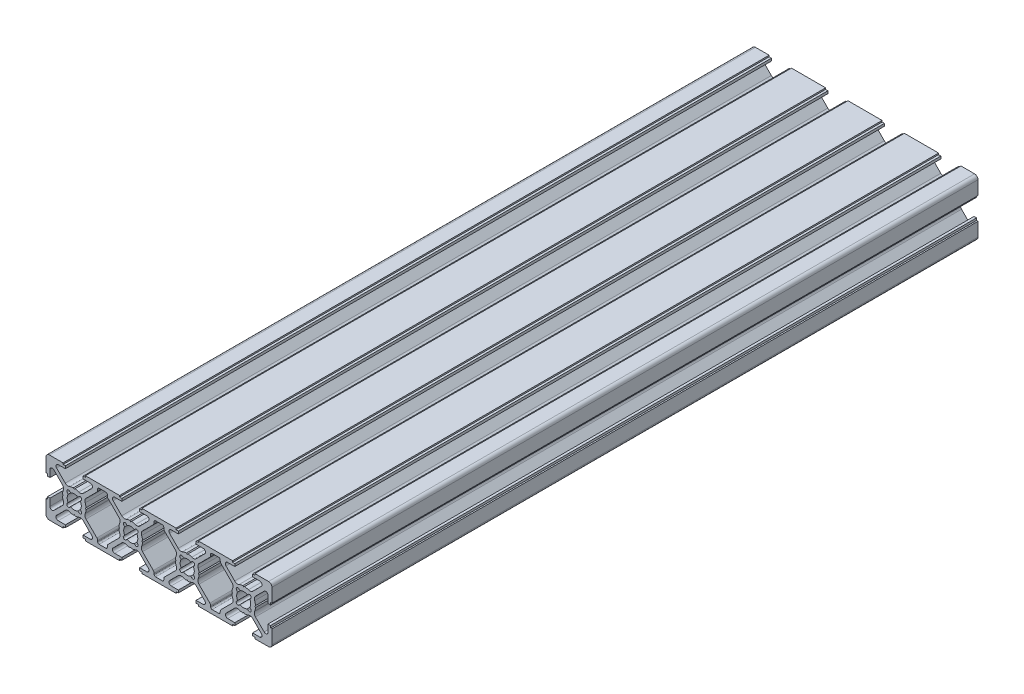
SolidWorks part; units mm, degrees
material "6063-T5"
ref_plane "Ön Düzlem" through (0, 0, 0) normal (0, 0, 1) x (1, 0, 0)
ref_plane "Üst Düzlem" through (0, 0, 0) normal (0, 1, 0) x (1, 0, 0)
ref_plane "Sağ Düzlem" through (0, 0, 0) normal (1, 0, 0) x (0, 0, -1)
sketch "Model" plane through (0, 0, 0) normal (0, 0, 1) x (1, 0, 0)
  line L0 (-8.8, -10) -> (-3.95, -10)
  line L1 (-3.95, -10) -> (-3.95, -9.5)
  line L2 (-3.95, -9.5) -> (-3.1475, -9.5)
  line L3 (-3.1475, -9.5) -> (-3.1475, -8.6)
  line L4 (-3.1475, -8.6) -> (-5.6787, -8.6)
  line L5 (-6.2444, -7.2343) -> (-3.1787, -4.1687)
  line L6 (-0.29, -4.19) -> (0, -3.9)
  line L7 (0, -3.9) -> (0.29, -4.19)
  line L8 (3.1768, -4.1667) -> (6.2444, -7.2343)
  line L9 (5.6787, -8.6) -> (3.1475, -8.6)
  line L10 (3.1475, -8.6) -> (3.1475, -9.5)
  line L11 (3.1475, -9.5) -> (3.95, -9.5)
  line L12 (3.95, -9.5) -> (3.95, -10)
  line L13 (3.95, -10) -> (16.05, -10)
  line L14 (16.05, -10) -> (16.05, -9.5)
  line L15 (16.05, -9.5) -> (16.8525, -9.5)
  line L16 (16.8525, -9.5) -> (16.8525, -8.6)
  line L17 (16.8525, -8.6) -> (14.3213, -8.6)
  line L18 (13.7556, -7.2343) -> (16.8213, -4.1687)
  line L19 (19.71, -4.19) -> (20, -3.9)
  line L20 (20, -3.9) -> (20.29, -4.19)
  line L21 (23.1768, -4.1667) -> (26.2444, -7.2343)
  line L22 (25.6787, -8.6) -> (23.1475, -8.6)
  line L23 (23.1475, -8.6) -> (23.1475, -9.5)
  line L24 (23.1475, -9.5) -> (23.95, -9.5)
  line L25 (23.95, -9.5) -> (23.95, -10)
  line L26 (23.95, -10) -> (36.05, -10)
  line L27 (36.05, -10) -> (36.05, -9.5)
  line L28 (36.05, -9.5) -> (36.8525, -9.5)
  line L29 (36.8525, -9.5) -> (36.8525, -8.6)
  line L30 (36.8525, -8.6) -> (34.3213, -8.6)
  line L31 (33.7556, -7.2343) -> (36.8213, -4.1687)
  line L32 (39.71, -4.19) -> (40, -3.9)
  line L33 (40, -3.9) -> (40.29, -4.19)
  line L34 (43.1768, -4.1667) -> (46.2444, -7.2343)
  line L35 (45.6787, -8.6) -> (43.1475, -8.6)
  line L36 (43.1475, -8.6) -> (43.1475, -9.5)
  line L37 (43.1475, -9.5) -> (43.95, -9.5)
  line L38 (43.95, -9.5) -> (43.95, -10)
  line L39 (43.95, -10) -> (56.05, -10)
  line L40 (56.05, -10) -> (56.05, -9.5)
  line L41 (56.05, -9.5) -> (56.8525, -9.5)
  line L42 (56.8525, -9.5) -> (56.8525, -8.6)
  line L43 (56.8525, -8.6) -> (54.3213, -8.6)
  line L44 (53.7556, -7.2343) -> (56.8213, -4.1687)
  line L45 (59.71, -4.19) -> (60, -3.9)
  line L46 (60, -3.9) -> (60.29, -4.19)
  line L47 (63.1768, -4.1667) -> (66.2444, -7.2343)
  line L48 (65.6787, -8.6) -> (63.1475, -8.6)
  line L49 (63.1475, -8.6) -> (63.1475, -9.5)
  line L50 (63.1475, -9.5) -> (63.95, -9.5)
  line L51 (63.95, -9.5) -> (63.95, -10)
  line L52 (63.95, -10) -> (68.8, -10)
  line L53 (70, -8.8) -> (70, -3.95)
  line L54 (70, -3.95) -> (69.5, -3.95)
  line L55 (69.5, -3.95) -> (69.5, -3.1477)
  line L56 (69.5, -3.1477) -> (68.6, -3.1477)
  line L57 (68.6, -3.1477) -> (68.6, -5.6787)
  line L58 (67.2343, -6.2444) -> (64.1687, -3.1787)
  line L59 (64.19, -0.29) -> (63.9, 0)
  line L60 (63.9, 0) -> (64.19, 0.29)
  line L61 (64.1667, 3.1768) -> (67.2343, 6.2444)
  line L62 (68.6, 5.6787) -> (68.6, 3.1475)
  line L63 (68.6, 3.1475) -> (69.5, 3.1475)
  line L64 (69.5, 3.1475) -> (69.5, 3.95)
  line L65 (69.5, 3.95) -> (70, 3.95)
  line L66 (70, 3.95) -> (70, 8.8)
  line L67 (68.8, 10) -> (63.95, 10)
  line L68 (63.95, 10) -> (63.95, 9.5)
  line L69 (63.95, 9.5) -> (63.1475, 9.5)
  line L70 (63.1475, 9.5) -> (63.1475, 8.6)
  line L71 (63.1475, 8.6) -> (65.6787, 8.6)
  line L72 (66.2444, 7.2343) -> (63.1768, 4.1667)
  line L73 (60.29, 4.19) -> (60, 3.9)
  line L74 (60, 3.9) -> (59.71, 4.19)
  line L75 (56.8213, 4.1687) -> (53.7556, 7.2343)
  line L76 (54.3213, 8.6) -> (56.8525, 8.6)
  line L77 (56.8525, 8.6) -> (56.8525, 9.5)
  line L78 (56.8525, 9.5) -> (56.05, 9.5)
  line L79 (56.05, 9.5) -> (56.05, 10)
  line L80 (56.05, 10) -> (43.95, 10)
  line L81 (43.95, 10) -> (43.95, 9.5)
  line L82 (43.95, 9.5) -> (43.1475, 9.5)
  line L83 (43.1475, 9.5) -> (43.1475, 8.6)
  line L84 (43.1475, 8.6) -> (45.6787, 8.6)
  line L85 (46.2444, 7.2343) -> (43.1768, 4.1667)
  line L86 (40.29, 4.19) -> (40, 3.9)
  line L87 (40, 3.9) -> (39.71, 4.19)
  line L88 (36.8213, 4.1687) -> (33.7556, 7.2343)
  line L89 (34.3213, 8.6) -> (36.8525, 8.6)
  line L90 (36.8525, 8.6) -> (36.8525, 9.5)
  line L91 (36.8525, 9.5) -> (36.05, 9.5)
  line L92 (36.05, 9.5) -> (36.05, 10)
  line L93 (36.05, 10) -> (23.95, 10)
  line L94 (23.95, 10) -> (23.95, 9.5)
  line L95 (23.95, 9.5) -> (23.1475, 9.5)
  line L96 (23.1475, 9.5) -> (23.1475, 8.6)
  line L97 (23.1475, 8.6) -> (25.6787, 8.6)
  line L98 (26.2444, 7.2343) -> (23.1768, 4.1667)
  line L99 (20.29, 4.19) -> (20, 3.9)
  line L100 (20, 3.9) -> (19.71, 4.19)
  line L101 (16.8213, 4.1687) -> (13.7556, 7.2343)
  line L102 (14.3213, 8.6) -> (16.8525, 8.6)
  line L103 (16.8525, 8.6) -> (16.8525, 9.5)
  line L104 (16.8525, 9.5) -> (16.05, 9.5)
  line L105 (16.05, 9.5) -> (16.05, 10)
  line L106 (16.05, 10) -> (3.95, 10)
  line L107 (3.95, 10) -> (3.95, 9.5)
  line L108 (3.95, 9.5) -> (3.1475, 9.5)
  line L109 (3.1475, 9.5) -> (3.1475, 8.6)
  line L110 (3.1475, 8.6) -> (5.6787, 8.6)
  line L111 (6.2444, 7.2343) -> (3.1768, 4.1667)
  line L112 (0.29, 4.19) -> (0, 3.9)
  line L113 (0, 3.9) -> (-0.29, 4.19)
  line L114 (-3.1787, 4.1687) -> (-6.2444, 7.2343)
  line L115 (-5.6787, 8.6) -> (-3.1475, 8.6)
  line L116 (-3.1475, 8.6) -> (-3.1475, 9.5)
  line L117 (-3.1475, 9.5) -> (-3.95, 9.5)
  line L118 (-3.95, 9.5) -> (-3.95, 10)
  line L119 (-3.95, 10) -> (-8.8, 10)
  line L120 (-10, 8.8) -> (-10, 3.95)
  line L121 (-10, 3.95) -> (-9.5, 3.95)
  line L122 (-9.5, 3.95) -> (-9.5, 3.1475)
  line L123 (-9.5, 3.1475) -> (-8.6, 3.1475)
  line L124 (-8.6, 3.1475) -> (-8.6, 5.6787)
  line L125 (-7.2343, 6.2444) -> (-4.1667, 3.1768)
  line L126 (-4.19, 0.29) -> (-3.9, 0)
  line L127 (-3.9, 0) -> (-4.19, -0.29)
  line L128 (-4.1687, -3.1787) -> (-7.2343, -6.2444)
  line L129 (-8.6, -5.6787) -> (-8.6, -3.1475)
  line L130 (-8.6, -3.1475) -> (-9.5, -3.1475)
  line L131 (-9.5, -3.1475) -> (-9.5, -3.95)
  line L132 (-9.5, -3.95) -> (-10, -3.95)
  line L133 (-10, -3.95) -> (-10, -8.8)
  line L134 (62.1404, 1.2918) -> (62.4749, 1.6263)
  line L135 (61.6263, 2.4749) -> (61.2918, 2.1404)
  line L136 (58.7082, 2.1404) -> (58.3737, 2.4749)
  line L137 (57.5251, 1.6263) -> (57.8596, 1.2918)
  line L138 (57.8596, -1.2918) -> (57.5251, -1.6263)
  line L139 (58.3737, -2.4749) -> (58.7082, -2.1404)
  line L140 (61.2918, -2.1404) -> (61.6263, -2.4749)
  line L141 (62.4749, -1.6263) -> (62.1404, -1.2918)
  line L142 (55.8342, -3.1759) -> (51.9899, -7.0201)
  line L143 (51.6971, -7.7272) -> (51.6971, -8.1)
  line L144 (51.1971, -8.6) -> (48.8029, -8.6)
  line L145 (48.3029, -8.1) -> (48.3029, -7.7272)
  line L146 (48.0101, -7.0201) -> (44.1658, -3.1759)
  line L147 (44.19, -0.29) -> (43.9, 0)
  line L148 (43.9, 0) -> (44.19, 0.29)
  line L149 (44.1658, 3.1759) -> (48.0101, 7.0201)
  line L150 (48.3029, 7.7272) -> (48.3029, 8.1)
  line L151 (48.8029, 8.6) -> (51.1971, 8.6)
  line L152 (51.6971, 8.1) -> (51.6971, 7.7272)
  line L153 (51.9899, 7.0201) -> (55.8342, 3.1759)
  line L154 (55.81, 0.29) -> (56.1, 0)
  line L155 (56.1, 0) -> (55.81, -0.29)
  line L156 (-2.1404, 1.2918) -> (-2.4749, 1.6263)
  line L157 (-1.6263, 2.4749) -> (-1.2918, 2.1404)
  line L158 (1.2918, 2.1404) -> (1.6263, 2.4749)
  line L159 (2.4749, 1.6263) -> (2.1404, 1.2918)
  line L160 (2.1404, -1.2918) -> (2.4749, -1.6263)
  line L161 (1.6263, -2.4749) -> (1.2918, -2.1404)
  line L162 (-1.2918, -2.1404) -> (-1.6263, -2.4749)
  line L163 (-2.4749, -1.6263) -> (-2.1404, -1.2918)
  line L164 (4.1658, -3.1759) -> (8.0101, -7.0201)
  line L165 (8.3029, -7.7272) -> (8.3029, -8.1)
  line L166 (8.8029, -8.6) -> (11.1971, -8.6)
  line L167 (11.6971, -8.1) -> (11.6971, -7.7272)
  line L168 (11.9899, -7.0201) -> (15.8342, -3.1759)
  line L169 (15.81, -0.29) -> (16.1, 0)
  line L170 (16.1, 0) -> (15.81, 0.29)
  line L171 (15.8342, 3.1759) -> (11.9899, 7.0201)
  line L172 (11.6971, 7.7272) -> (11.6971, 8.1)
  line L173 (11.1971, 8.6) -> (8.8029, 8.6)
  line L174 (8.3029, 8.1) -> (8.3029, 7.7272)
  line L175 (8.0101, 7.0201) -> (4.1658, 3.1759)
  line L176 (4.19, 0.29) -> (3.9, 0)
  line L177 (3.9, 0) -> (4.19, -0.29)
  line L178 (17.8596, 1.2918) -> (17.5251, 1.6263)
  line L179 (18.3737, 2.4749) -> (18.7082, 2.1404)
  line L180 (21.2918, 2.1404) -> (21.6263, 2.4749)
  line L181 (22.4749, 1.6263) -> (22.1404, 1.2918)
  line L182 (22.1404, -1.2918) -> (22.4749, -1.6263)
  line L183 (21.6263, -2.4749) -> (21.2918, -2.1404)
  line L184 (18.7082, -2.1404) -> (18.3737, -2.4749)
  line L185 (17.5251, -1.6263) -> (17.8596, -1.2918)
  line L186 (37.8596, 1.2918) -> (37.5251, 1.6263)
  line L187 (38.3737, 2.4749) -> (38.7082, 2.1404)
  line L188 (41.2918, 2.1404) -> (41.6263, 2.4749)
  line L189 (42.4749, 1.6263) -> (42.1404, 1.2918)
  line L190 (42.1404, -1.2918) -> (42.4749, -1.6263)
  line L191 (41.6263, -2.4749) -> (41.2918, -2.1404)
  line L192 (38.7082, -2.1404) -> (38.3737, -2.4749)
  line L193 (37.5251, -1.6263) -> (37.8596, -1.2918)
  line L194 (24.1658, -3.1759) -> (28.0101, -7.0201)
  line L195 (28.3029, -7.7272) -> (28.3029, -8.1)
  line L196 (28.8029, -8.6) -> (31.1971, -8.6)
  line L197 (31.6971, -8.1) -> (31.6971, -7.7272)
  line L198 (31.9899, -7.0201) -> (35.8342, -3.1759)
  line L199 (35.81, -0.29) -> (36.1, 0)
  line L200 (36.1, 0) -> (35.81, 0.29)
  line L201 (35.8342, 3.1759) -> (31.9899, 7.0201)
  line L202 (31.6971, 7.7272) -> (31.6971, 8.1)
  line L203 (31.1971, 8.6) -> (28.8029, 8.6)
  line L204 (28.3029, 8.1) -> (28.3029, 7.7272)
  line L205 (28.0101, 7.0201) -> (24.1658, 3.1759)
  line L206 (24.19, 0.29) -> (23.9, 0)
  line L207 (23.9, 0) -> (24.19, -0.29)
  arc A0 (-6.2444, -7.2343) -> (-5.6787, -8.6) centre (-5.6787, -7.8) ccw
  arc A1 (-1.6394, -3.8668) -> (-3.1787, -4.1687) centre (-2.1845, -5.1629) ccw
  arc A2 (-1.6394, -3.8668) -> (-0.29, -4.19) centre (0, 0) ccw
  arc A3 (0.29, -4.19) -> (1.6394, -3.8668) centre (0, 0) ccw
  arc A4 (3.1768, -4.1667) -> (1.6394, -3.8668) centre (2.1855, -5.1581) ccw
  arc A5 (5.6787, -8.6) -> (6.2444, -7.2343) centre (5.6787, -7.8) ccw
  arc A6 (13.7556, -7.2343) -> (14.3213, -8.6) centre (14.3213, -7.8) ccw
  arc A7 (18.3606, -3.8668) -> (16.8213, -4.1687) centre (17.8155, -5.1629) ccw
  arc A8 (18.3606, -3.8668) -> (19.71, -4.19) centre (20, 0) ccw
  arc A9 (20.29, -4.19) -> (21.6394, -3.8668) centre (20, 0) ccw
  arc A10 (23.1768, -4.1667) -> (21.6394, -3.8668) centre (22.1855, -5.1581) ccw
  arc A11 (25.6787, -8.6) -> (26.2444, -7.2343) centre (25.6787, -7.8) ccw
  arc A12 (33.7556, -7.2343) -> (34.3213, -8.6) centre (34.3213, -7.8) ccw
  arc A13 (38.3606, -3.8668) -> (36.8213, -4.1687) centre (37.8155, -5.1629) ccw
  arc A14 (38.3606, -3.8668) -> (39.71, -4.19) centre (40, 0) ccw
  arc A15 (40.29, -4.19) -> (41.6394, -3.8668) centre (40, 0) ccw
  arc A16 (43.1768, -4.1667) -> (41.6394, -3.8668) centre (42.1855, -5.1581) ccw
  arc A17 (45.6787, -8.6) -> (46.2444, -7.2343) centre (45.6787, -7.8) ccw
  arc A18 (53.7556, -7.2343) -> (54.3213, -8.6) centre (54.3213, -7.8) ccw
  arc A19 (58.3606, -3.8668) -> (56.8213, -4.1687) centre (57.8155, -5.1629) ccw
  arc A20 (58.3606, -3.8668) -> (59.71, -4.19) centre (60, 0) ccw
  arc A21 (60.29, -4.19) -> (61.6394, -3.8668) centre (60, 0) ccw
  arc A22 (63.1768, -4.1667) -> (61.6394, -3.8668) centre (62.1855, -5.1581) ccw
  arc A23 (65.6787, -8.6) -> (66.2444, -7.2343) centre (65.6787, -7.8) ccw
  arc A24 (68.8, -10) -> (70, -8.8) centre (68.8, -8.8) ccw
  arc A25 (67.2343, -6.2444) -> (68.6, -5.6787) centre (67.8, -5.6787) ccw
  arc A26 (63.8668, -1.6394) -> (64.1687, -3.1787) centre (65.1629, -2.1845) ccw
  arc A27 (63.8668, -1.6394) -> (64.19, -0.29) centre (60, 0) ccw
  arc A28 (64.19, 0.29) -> (63.8668, 1.6394) centre (60, 0) ccw
  arc A29 (64.1667, 3.1768) -> (63.8668, 1.6394) centre (65.1581, 2.1855) ccw
  arc A30 (68.6, 5.6787) -> (67.2343, 6.2444) centre (67.8, 5.6787) ccw
  arc A31 (70, 8.8) -> (68.8, 10) centre (68.8, 8.8) ccw
  arc A32 (66.2444, 7.2343) -> (65.6787, 8.6) centre (65.6787, 7.8) ccw
  arc A33 (61.6394, 3.8668) -> (63.1768, 4.1667) centre (62.1855, 5.1581) ccw
  arc A34 (61.6394, 3.8668) -> (60.29, 4.19) centre (60, 0) ccw
  arc A35 (59.71, 4.19) -> (58.3606, 3.8668) centre (60, 0) ccw
  arc A36 (56.8213, 4.1687) -> (58.3606, 3.8668) centre (57.8155, 5.1629) ccw
  arc A37 (54.3213, 8.6) -> (53.7556, 7.2343) centre (54.3213, 7.8) ccw
  arc A38 (46.2444, 7.2343) -> (45.6787, 8.6) centre (45.6787, 7.8) ccw
  arc A39 (41.6394, 3.8668) -> (43.1768, 4.1667) centre (42.1855, 5.1581) ccw
  arc A40 (41.6394, 3.8668) -> (40.29, 4.19) centre (40, 0) ccw
  arc A41 (39.71, 4.19) -> (38.3606, 3.8668) centre (40, 0) ccw
  arc A42 (36.8213, 4.1687) -> (38.3606, 3.8668) centre (37.8155, 5.1629) ccw
  arc A43 (34.3213, 8.6) -> (33.7556, 7.2343) centre (34.3213, 7.8) ccw
  arc A44 (26.2444, 7.2343) -> (25.6787, 8.6) centre (25.6787, 7.8) ccw
  arc A45 (21.6394, 3.8668) -> (23.1768, 4.1667) centre (22.1855, 5.1581) ccw
  arc A46 (21.6394, 3.8668) -> (20.29, 4.19) centre (20, 0) ccw
  arc A47 (19.71, 4.19) -> (18.3606, 3.8668) centre (20, 0) ccw
  arc A48 (16.8213, 4.1687) -> (18.3606, 3.8668) centre (17.8155, 5.1629) ccw
  arc A49 (14.3213, 8.6) -> (13.7556, 7.2343) centre (14.3213, 7.8) ccw
  arc A50 (6.2444, 7.2343) -> (5.6787, 8.6) centre (5.6787, 7.8) ccw
  arc A51 (1.6394, 3.8668) -> (3.1768, 4.1667) centre (2.1855, 5.1581) ccw
  arc A52 (1.6394, 3.8668) -> (0.29, 4.19) centre (0, 0) ccw
  arc A53 (-0.29, 4.19) -> (-1.6394, 3.8668) centre (0, 0) ccw
  arc A54 (-3.1787, 4.1687) -> (-1.6394, 3.8668) centre (-2.1845, 5.1629) ccw
  arc A55 (-5.6787, 8.6) -> (-6.2444, 7.2343) centre (-5.6787, 7.8) ccw
  arc A56 (-8.8, 10) -> (-10, 8.8) centre (-8.8, 8.8) ccw
  arc A57 (-7.2343, 6.2444) -> (-8.6, 5.6787) centre (-7.8, 5.6787) ccw
  arc A58 (-3.8668, 1.6394) -> (-4.1667, 3.1768) centre (-5.1581, 2.1855) ccw
  arc A59 (-3.8668, 1.6394) -> (-4.19, 0.29) centre (0, 0) ccw
  arc A60 (-4.19, -0.29) -> (-3.8668, -1.6394) centre (0, 0) ccw
  arc A61 (-4.1687, -3.1787) -> (-3.8668, -1.6394) centre (-5.1629, -2.1845) ccw
  arc A62 (-8.6, -5.6787) -> (-7.2343, -6.2444) centre (-7.8, -5.6787) ccw
  arc A63 (-10, -8.8) -> (-8.8, -10) centre (-8.8, -8.8) ccw
  arc A64 (51.9899, -7.0201) -> (51.6971, -7.7272) centre (52.6971, -7.7272) ccw
  arc A65 (51.1971, -8.6) -> (51.6971, -8.1) centre (51.1971, -8.1) ccw
  arc A66 (48.3029, -8.1) -> (48.8029, -8.6) centre (48.8029, -8.1) ccw
  arc A67 (48.3029, -7.7272) -> (48.0101, -7.0201) centre (47.3029, -7.7272) ccw
  arc A68 (43.8668, -1.6394) -> (44.1658, -3.1759) centre (45.1558, -2.1859) ccw
  arc A69 (43.8668, -1.6394) -> (44.19, -0.29) centre (40, 0) ccw
  arc A70 (44.19, 0.29) -> (43.8668, 1.6394) centre (40, 0) ccw
  arc A71 (44.1658, 3.1759) -> (43.8668, 1.6394) centre (45.1558, 2.1859) ccw
  arc A72 (48.0101, 7.0201) -> (48.3029, 7.7272) centre (47.3029, 7.7272) ccw
  arc A73 (48.8029, 8.6) -> (48.3029, 8.1) centre (48.8029, 8.1) ccw
  arc A74 (51.6971, 8.1) -> (51.1971, 8.6) centre (51.1971, 8.1) ccw
  arc A75 (51.6971, 7.7272) -> (51.9899, 7.0201) centre (52.6971, 7.7272) ccw
  arc A76 (56.1332, 1.6394) -> (55.8342, 3.1759) centre (54.8442, 2.1859) ccw
  arc A77 (56.1332, 1.6394) -> (55.81, 0.29) centre (60, 0) ccw
  arc A78 (55.81, -0.29) -> (56.1332, -1.6394) centre (60, 0) ccw
  arc A79 (55.8342, -3.1759) -> (56.1332, -1.6394) centre (54.8442, -2.1859) ccw
  arc A80 (8.3029, -7.7272) -> (8.0101, -7.0201) centre (7.3029, -7.7272) ccw
  arc A81 (8.3029, -8.1) -> (8.8029, -8.6) centre (8.8029, -8.1) ccw
  arc A82 (11.1971, -8.6) -> (11.6971, -8.1) centre (11.1971, -8.1) ccw
  arc A83 (11.9899, -7.0201) -> (11.6971, -7.7272) centre (12.6971, -7.7272) ccw
  arc A84 (15.8342, -3.1759) -> (16.1332, -1.6394) centre (14.8442, -2.1859) ccw
  arc A85 (15.81, -0.29) -> (16.1332, -1.6394) centre (20, 0) ccw
  arc A86 (16.1332, 1.6394) -> (15.81, 0.29) centre (20, 0) ccw
  arc A87 (16.1332, 1.6394) -> (15.8342, 3.1759) centre (14.8442, 2.1859) ccw
  arc A88 (11.6971, 7.7272) -> (11.9899, 7.0201) centre (12.6971, 7.7272) ccw
  arc A89 (11.6971, 8.1) -> (11.1971, 8.6) centre (11.1971, 8.1) ccw
  arc A90 (8.8029, 8.6) -> (8.3029, 8.1) centre (8.8029, 8.1) ccw
  arc A91 (8.0101, 7.0201) -> (8.3029, 7.7272) centre (7.3029, 7.7272) ccw
  arc A92 (4.1658, 3.1759) -> (3.8668, 1.6394) centre (5.1558, 2.1859) ccw
  arc A93 (4.19, 0.29) -> (3.8668, 1.6394) centre (0, 0) ccw
  arc A94 (3.8668, -1.6394) -> (4.19, -0.29) centre (0, 0) ccw
  arc A95 (3.8668, -1.6394) -> (4.1658, -3.1759) centre (5.1558, -2.1859) ccw
  arc A96 (28.3029, -7.7272) -> (28.0101, -7.0201) centre (27.3029, -7.7272) ccw
  arc A97 (28.3029, -8.1) -> (28.8029, -8.6) centre (28.8029, -8.1) ccw
  arc A98 (31.1971, -8.6) -> (31.6971, -8.1) centre (31.1971, -8.1) ccw
  arc A99 (31.9899, -7.0201) -> (31.6971, -7.7272) centre (32.6971, -7.7272) ccw
  arc A100 (35.8342, -3.1759) -> (36.1332, -1.6394) centre (34.8442, -2.1859) ccw
  arc A101 (35.81, -0.29) -> (36.1332, -1.6394) centre (40, 0) ccw
  arc A102 (36.1332, 1.6394) -> (35.81, 0.29) centre (40, 0) ccw
  arc A103 (36.1332, 1.6394) -> (35.8342, 3.1759) centre (34.8442, 2.1859) ccw
  arc A104 (31.6971, 7.7272) -> (31.9899, 7.0201) centre (32.6971, 7.7272) ccw
  arc A105 (31.6971, 8.1) -> (31.1971, 8.6) centre (31.1971, 8.1) ccw
  arc A106 (28.8029, 8.6) -> (28.3029, 8.1) centre (28.8029, 8.1) ccw
  arc A107 (28.0101, 7.0201) -> (28.3029, 7.7272) centre (27.3029, 7.7272) ccw
  arc A108 (24.1658, 3.1759) -> (23.8668, 1.6394) centre (25.1558, 2.1859) ccw
  arc A109 (24.19, 0.29) -> (23.8668, 1.6394) centre (20, 0) ccw
  arc A110 (23.8668, -1.6394) -> (24.19, -0.29) centre (20, 0) ccw
  arc A111 (23.8668, -1.6394) -> (24.1658, -3.1759) centre (25.1558, -2.1859) ccw
  arc A112 (62.4749, 1.6263) -> (61.6263, 2.4749) centre (62.0506, 2.0506) ccw
  arc A113 (61.2918, 2.1404) -> (58.7082, 2.1404) centre (60, 0) ccw
  arc A114 (58.3737, 2.4749) -> (57.5251, 1.6263) centre (57.9494, 2.0506) ccw
  arc A115 (57.8596, 1.2918) -> (57.8596, -1.2918) centre (60, 0) ccw
  arc A116 (57.5251, -1.6263) -> (58.3737, -2.4749) centre (57.9494, -2.0506) ccw
  arc A117 (58.7082, -2.1404) -> (61.2918, -2.1404) centre (60, 0) ccw
  arc A118 (61.6263, -2.4749) -> (62.4749, -1.6263) centre (62.0506, -2.0506) ccw
  arc A119 (62.1404, -1.2918) -> (62.1404, 1.2918) centre (60, 0) ccw
  arc A120 (-1.6263, 2.4749) -> (-2.4749, 1.6263) centre (-2.0506, 2.0506) ccw
  arc A121 (1.2918, 2.1404) -> (-1.2918, 2.1404) centre (0, 0) ccw
  arc A122 (2.4749, 1.6263) -> (1.6263, 2.4749) centre (2.0506, 2.0506) ccw
  arc A123 (2.1404, -1.2918) -> (2.1404, 1.2918) centre (0, 0) ccw
  arc A124 (1.6263, -2.4749) -> (2.4749, -1.6263) centre (2.0506, -2.0506) ccw
  arc A125 (-1.2918, -2.1404) -> (1.2918, -2.1404) centre (0, 0) ccw
  arc A126 (-2.4749, -1.6263) -> (-1.6263, -2.4749) centre (-2.0506, -2.0506) ccw
  arc A127 (-2.1404, 1.2918) -> (-2.1404, -1.2918) centre (0, 0) ccw
  arc A128 (18.3737, 2.4749) -> (17.5251, 1.6263) centre (17.9494, 2.0506) ccw
  arc A129 (21.2918, 2.1404) -> (18.7082, 2.1404) centre (20, 0) ccw
  arc A130 (22.4749, 1.6263) -> (21.6263, 2.4749) centre (22.0506, 2.0506) ccw
  arc A131 (22.1404, -1.2918) -> (22.1404, 1.2918) centre (20, 0) ccw
  arc A132 (21.6263, -2.4749) -> (22.4749, -1.6263) centre (22.0506, -2.0506) ccw
  arc A133 (18.7082, -2.1404) -> (21.2918, -2.1404) centre (20, 0) ccw
  arc A134 (17.5251, -1.6263) -> (18.3737, -2.4749) centre (17.9494, -2.0506) ccw
  arc A135 (17.8596, 1.2918) -> (17.8596, -1.2918) centre (20, 0) ccw
  arc A136 (38.3737, 2.4749) -> (37.5251, 1.6263) centre (37.9494, 2.0506) ccw
  arc A137 (41.2918, 2.1404) -> (38.7082, 2.1404) centre (40, 0) ccw
  arc A138 (42.4749, 1.6263) -> (41.6263, 2.4749) centre (42.0506, 2.0506) ccw
  arc A139 (42.1404, -1.2918) -> (42.1404, 1.2918) centre (40, 0) ccw
  arc A140 (41.6263, -2.4749) -> (42.4749, -1.6263) centre (42.0506, -2.0506) ccw
  arc A141 (38.7082, -2.1404) -> (41.2918, -2.1404) centre (40, 0) ccw
  arc A142 (37.5251, -1.6263) -> (38.3737, -2.4749) centre (37.9494, -2.0506) ccw
  arc A143 (37.8596, 1.2918) -> (37.8596, -1.2918) centre (40, 0) ccw
extrude "Yükseklik-Ekstrüzyon1" add sketch "Model" against normal blind 250
